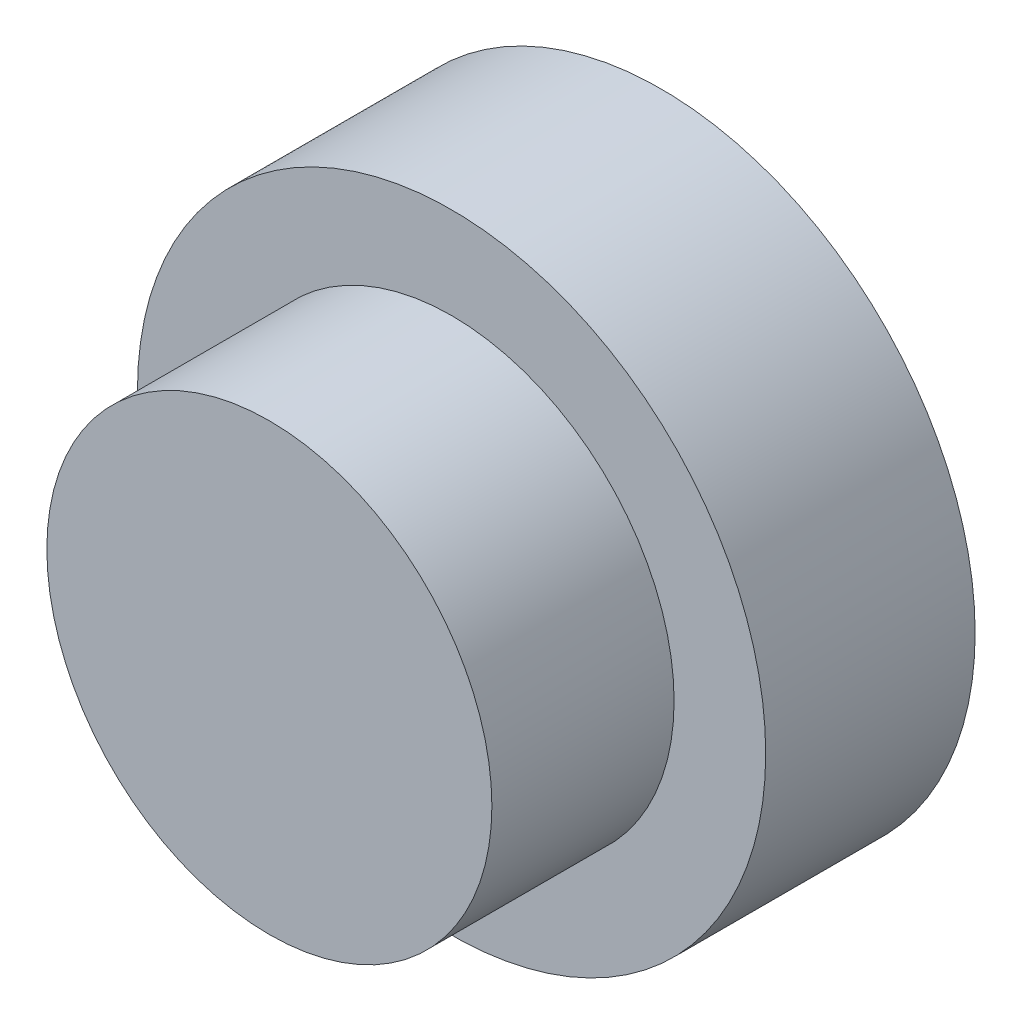
SolidWorks part; units mm, degrees
ref_plane "Front Plane" through (0, 0, 0) normal (0, 0, 1) x (1, 0, 0)
ref_plane "Top Plane" through (0, 0, 0) normal (0, 1, 0) x (1, 0, 0)
ref_plane "Right Plane" through (0, 0, 0) normal (1, 0, 0) x (0, 0, -1)
sketch "Sketch1" plane through (0, 0, 0) normal (0, 0, 1) x (1, 0, 0)
  circle A0 centre (0, 0) radius 38.1
  circle A1 centre (0, 0) radius 9.525
  dimension "D1" = 76.2
  dimension "D2" = 19.05
extrude "Boss-Extrude1" add sketch "Sketch1" along normal blind 25.4
sketch "Sketch2" plane through (0, 0, 0) normal (0, 0, -1) x (-1, 0, 0)
  circle A0 centre (0, 0) radius 26.9875
  dimension "D1" = 53.975
extrude "Boss-Extrude3" add sketch "Sketch2" against normal blind 47.498
